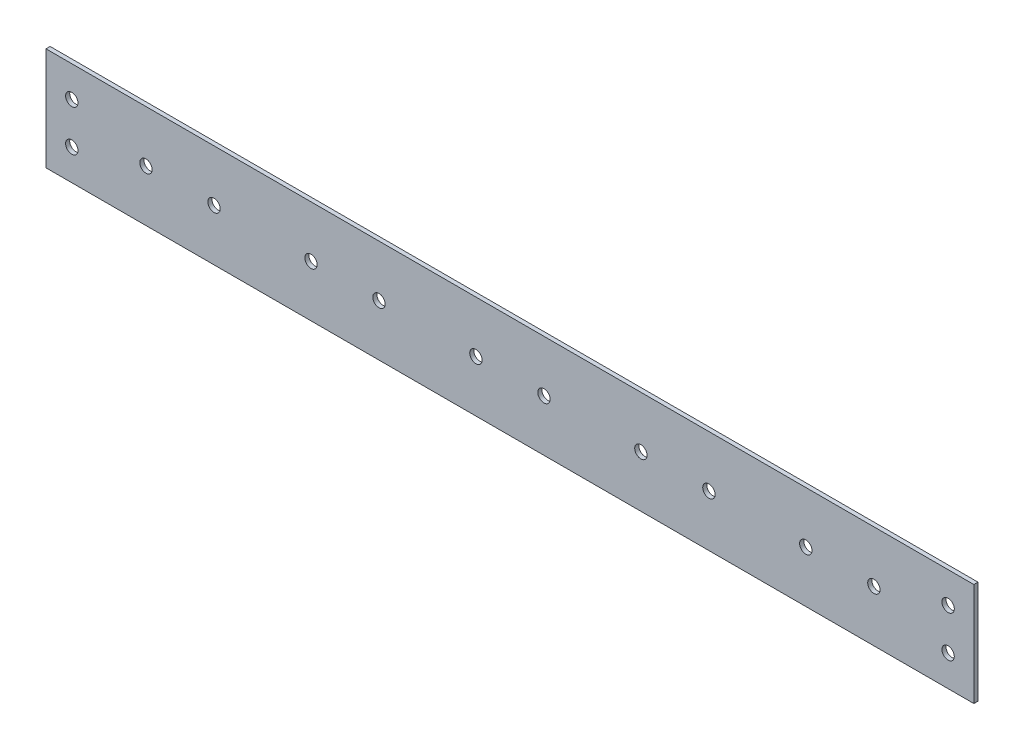
SolidWorks part; units mm, degrees
ref_plane "Спереди" through (0, 0, 0) normal (0, 0, 1) x (1, 0, 0)
ref_plane "Сверху" through (0, 0, 0) normal (0, 1, 0) x (1, 0, 0)
ref_plane "Справа" through (0, 0, 0) normal (1, 0, 0) x (0, 0, -1)
sketch "Эскиз1" plane through (0, 0, 0) normal (0, 0, 1) x (1, 0, 0)
  line L0 (-53.858, -2.6022) -> (396.142, -2.6022) construction
  line L1 (-53.858, 22.3978) -> (396.142, 22.3978)
  line L2 (-53.858, 22.3978) -> (-53.858, -27.6022)
  line L3 (-53.858, -27.6022) -> (396.142, -27.6022)
  line L4 (396.142, 22.3978) -> (396.142, -27.6022)
  circle A0 centre (-5.358, -2.6022) radius 3
  circle A1 centre (27.642, -2.6022) radius 3
  circle A2 centre (74.642, -2.6022) radius 3
  circle A3 centre (107.642, -2.6022) radius 3
  circle A4 centre (154.642, -2.6022) radius 3
  circle A5 centre (187.642, -2.6022) radius 3
  circle A6 centre (234.642, -2.6022) radius 3
  circle A7 centre (267.642, -2.6022) radius 3
  circle A8 centre (314.642, -2.6022) radius 3
  circle A9 centre (347.642, -2.6022) radius 3
  dimension "D3" = 2
  dimension "D6" = 48.5
  dimension "D1" = 50
  dimension "D2" = 450
  dimension "D4" = 48.5
  dimension "D5" = 5
extrude "Бобышка-Вытянуть1" add sketch "Эскиз1" along normal blind 2
sketch "Эскиз2" plane through (0, 0, 2) normal (0, 0, 1) x (1, 0, 0)
  line L0 (-53.858, 22.3978) -> (-53.858, -27.6022) construction
  line L1 (396.142, 22.3978) -> (-53.858, 22.3978) construction
  line L2 (-53.858, -27.6022) -> (396.142, -27.6022) construction
  line L4 (-41.358, 22.3978) -> (-41.358, -27.6022) construction
  line L5 (-53.858, -2.6022) -> (-31.4802, -2.6022) construction
  line L6 (171.142, 22.3978) -> (171.142, -27.6022) construction
  circle A0 centre (-41.358, 7.3978) radius 3
  circle A1 centre (-41.358, -12.6022) radius 3
  circle A2 centre (383.642, -12.6022) radius 3
  circle A3 centre (383.642, 7.3978) radius 3
  dimension "D2" = 15
  dimension "D1" = 12.5
extrude "Вырез-Вытянуть1" cut sketch "Эскиз2" against normal through all
